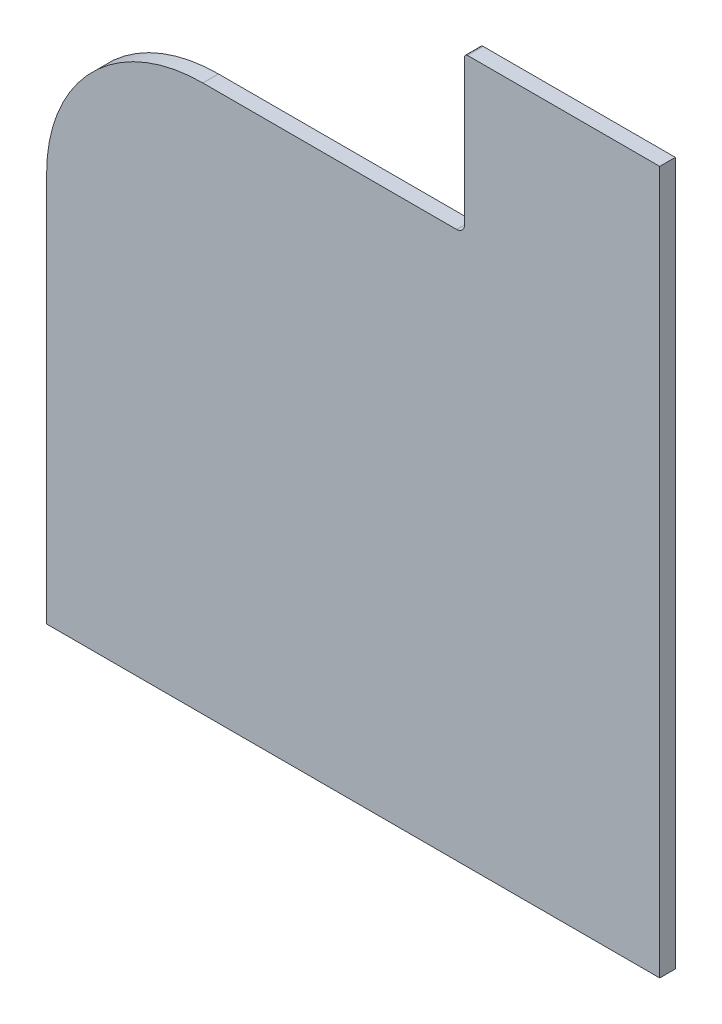
SolidWorks part; units mm, degrees
ref_plane "Ön Düzlem" through (0, 0, 0) normal (0, 0, 1) x (1, 0, 0)
ref_plane "Üst Düzlem" through (0, 0, 0) normal (0, 1, 0) x (1, 0, 0)
ref_plane "Sağ Düzlem" through (0, 0, 0) normal (1, 0, 0) x (0, 0, -1)
sketch "Sketch1" plane through (0, 0, 0) normal (0, 0, 1) x (1, 0, 0)
  line L0 (-300, 400) -> (25, 400)
  line L2 (-500, 200) -> (-500, -300)
  line L3 (-500, -300) -> (285, -300)
  line L4 (285, 100) -> (285, -300)
  line L5 (35, 600) -> (35, 410)
  line L8 (285, 100) -> (285, 600)
  line L9 (285, 600) -> (35, 600)
  arc A0 (-300, 400) -> (-500, 200) centre (-300, 200) ccw
  arc A1 (35, 410) -> (25, 400) centre (25, 410) cw
  point P0 (0, 0)
  point P17 (35, 600)
  dimension "D3" = 200
  dimension "D6" = 10
  dimension "D1" = 400
  dimension "D2" = 785
  dimension "D4" = 200
  dimension "D5" = 250
  dimension "D7" = 500
extrude "Boss-Extrude1" add sketch "Sketch1" along normal blind 20
fillet "Fillet1" radius 4 1 edges at (35, 600, 10)
